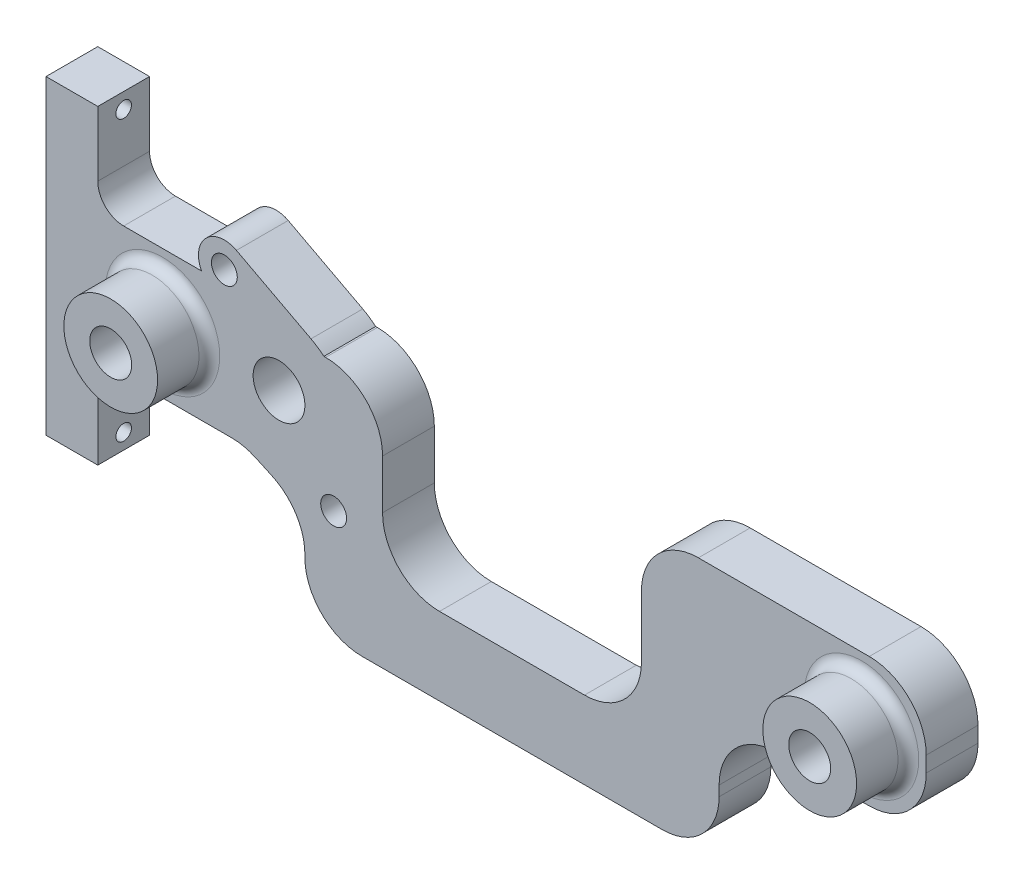
SolidWorks part; units mm, degrees
ref_plane "Front Plane" through (0, 0, 0) normal (0, 0, 1) x (1, 0, 0)
ref_plane "Top Plane" through (0, 0, 0) normal (0, 1, 0) x (1, 0, 0)
ref_plane "Right Plane" through (0, 0, 0) normal (1, 0, 0) x (0, 0, -1)
sketch "Sketch1" plane through (0, 0, 0) normal (0, 0, 1) x (1, 0, 0)
  line L0 (-67.5, 0) -> (67.5, 0) construction
  line L1 (-80, -12.5) -> (-51.7726, -12.5)
  line L2 (-80, -12.5) -> (-80, 12.5)
  line L3 (-80, 12.5) -> (-59.9471, 12.5)
  line L4 (80, -12.5) -> (80, 12.5)
  line L5 (-80, -12.5) -> (80, 12.5) construction
  line L6 (-80, 12.5) -> (80, -12.5) construction
  line L7 (40, -36.4616) -> (-40, -36.4616)
  line L8 (0, -43.218) -> (0, 21.5233) construction
  line L9 (-40, -36.4616) -> (-40, -17.8549)
  line L10 (-25, 10.0239) -> (-25, -21.4616)
  line L11 (-25, -21.4616) -> (25, -21.4616)
  line L12 (25, -21.4616) -> (25, 12.5)
  line L13 (40, -36.4616) -> (40, -12.5)
  line L14 (25, 12.5) -> (80, 12.5)
  line L15 (40, -12.5) -> (80, -12.5)
  line L16 (-55.5544, 14.8885) -> (-34.4456, -14.8885) construction
  line L18 (-51.7726, -12.5) -> (-40, -17.8549)
  line L20 (-38.8216, 11.7193) -> (-53.2226, 19.3115)
  line L22 (-36.3377, 10.0239) -> (-25, 10.0239)
  circle A0 centre (-67.5, 0) radius 4.05
  circle A1 centre (67.5, 0) radius 4.05
  circle A2 centre (-45, 0) radius 5
  circle A3 centre (-34.4456, -14.8885) radius 2.5
  circle A4 centre (-55.5544, 14.8885) radius 2.5
  arc A10 (-53.2226, 19.3115) -> (-59.9471, 12.5) centre (-55.5544, 14.8885) ccw
  arc A12 (-36.3377, 10.0239) -> (-38.8216, 11.7193) centre (-45, 0) ccw
  point P0 (0, 0)
  point P7 (0, 0)
  point P16 (0, -36.4616)
  point P20 (0, -21.4616)
  point P28 (-45, 0)
  dimension "D4" = 8.1
  dimension "D5" = 10
  dimension "D11" = 5
  dimension "D13" = 80
  dimension "D14" = 10
  dimension "D1" = 160
  dimension "D2" = 25
  dimension "D3" = 135
  dimension "D6" = 35
  dimension "D7" = 80
  dimension "D8" = 15
  dimension "D9" = 50
  dimension "D10" = 36.5
extrude "Boss-Extrude1" add sketch "Sketch1" along normal blind 10
fillet "Fillet1" radius 11 11 edges at (40, -12.5, 5) (-25, -21.4616, 5) (25, -21.4616, 5) (40, -36.4616, 5) (-40, -36.4616, 5) (-51.7726, -12.5, 5) (-40, -17.8549, 5) (-25, 10.0239, 5) (80, -12.5, 5) (80, 12.5, 5) (25, 12.5, 5)
sketch "Sketch2" plane through (0, 0, 10) normal (0, 0, 1) x (1, 0, 0)
  circle A0 centre (67.5, 0) radius 4.05 construction
  circle A1 centre (-67.5, 0) radius 4.05 construction
  circle A2 centre (67.5, 0) radius 4.05
  circle A3 centre (-67.5, 0) radius 4.05
  circle A4 centre (-67.5, 0) radius 9.05
  circle A5 centre (67.5, 0) radius 9.05
  dimension "D1" = 5
extrude "Boss-Extrude2" add sketch "Sketch2" along normal blind 10
fillet "Fillet2" radius 2 2 edges at (-58.45, 0, 10) (76.55, 0, 10)
sketch "Sketch3" plane through (-80, 0, 0) normal (-1, 0, 0) x (0, 0, 1)
  line L0 (0, 12.5) -> (0, -12.5) construction
  line L1 (0, -30) -> (10, -30)
  line L2 (0, -30) -> (0, 30)
  line L3 (0, 30) -> (10, 30)
  line L4 (10, -30) -> (10, 30)
  point P9 (0, 0)
  point P12 (0, 0)
  dimension "D1" = 60
extrude "Boss-Extrude3" add sketch "Sketch3" along normal blind 10
fillet "Fillet3" radius 5 2 edges at (-80, -12.5, 5) (-80, 12.5, 5)
sketch "Sketch4" plane through (-90, 0, 0) normal (-1, 0, 0) x (0, 0, 1)
  line L0 (5, 30) -> (5, -30) construction
  line L1 (10, 30) -> (0, 30) construction
  line L2 (0, -30) -> (10, -30) construction
  line L3 (0, 0) -> (10, 0) construction
  line L4 (0, 30) -> (0, -30) construction
  line L5 (10, -11.05) -> (10, 11.05) construction
  circle A0 centre (5, 27) radius 1.5
  circle A1 centre (5, -27) radius 1.5
  dimension "D1" = 3
  dimension "D2" = 3
extrude "Cut-Extrude1" cut sketch "Sketch4" against normal blind 10
